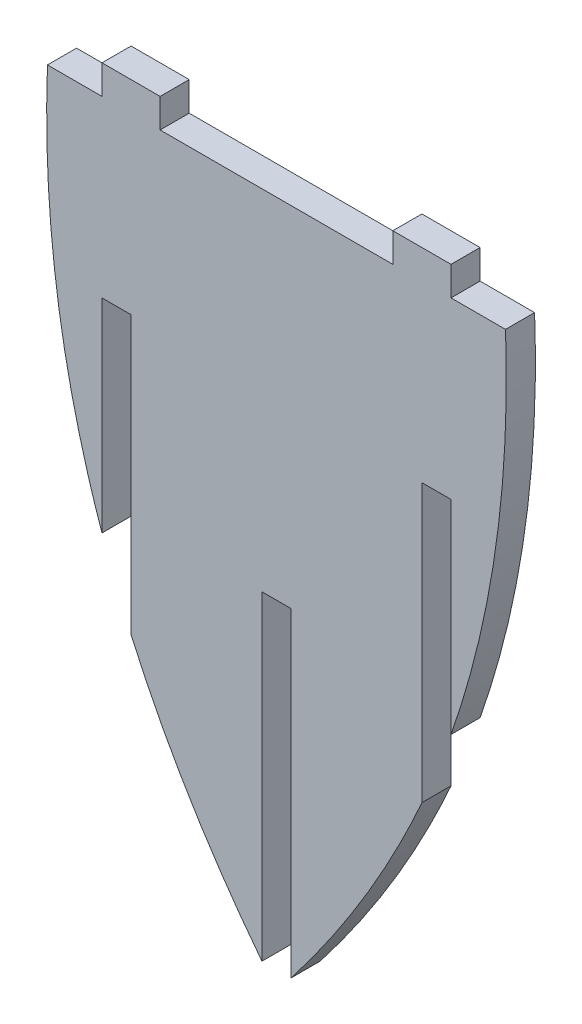
SolidWorks part; units mm, degrees
ref_plane "Front Plane" through (0, 0, 0) normal (0, 0, 1) x (1, 0, 0)
ref_plane "Top Plane" through (0, 0, 0) normal (0, 1, 0) x (1, 0, 0)
ref_plane "Right Plane" through (0, 0, 0) normal (1, 0, 0) x (0, 0, -1)
sketch "Sketch1" plane through (0, 0, 0) normal (0, 0, 1) x (1, 0, 0)
  line L0 (-53.175, 406.4) -> (-41.275, 406.4)
  line L1 (-41.275, 412.75) -> (-28.575, 412.75)
  line L2 (-34.925, 368.3) -> (-34.925, 307.7927)
  line L3 (-41.275, 323.85) -> (-41.275, 368.3)
  line L4 (-41.275, 368.3) -> (-34.925, 368.3)
  line L5 (-53.175, 406.4) -> (-8.275, 406.4) construction
  line L6 (-41.275, 406.4) -> (-41.275, 412.75)
  line L7 (-6.35, 260.35) -> (-6.35, 330.2)
  line L8 (-28.575, 412.75) -> (-28.575, 406.4)
  line L9 (-28.575, 406.4) -> (-6.35, 406.4)
  line L10 (-3.175, 274.1399) -> (-3.175, 422.7876) construction
  line L11 (22.225, 412.75) -> (34.925, 412.75)
  line L12 (22.225, 412.75) -> (22.225, 406.4)
  line L13 (-6.35, 330.2) -> (0, 330.2)
  line L14 (34.925, 406.4) -> (34.925, 412.75)
  line L15 (22.225, 406.4) -> (-6.35, 406.4)
  line L16 (34.925, 406.4) -> (46.825, 406.4)
  line L17 (0, 330.2) -> (0, 260.35)
  line L18 (28.575, 368.3) -> (28.575, 307.7927)
  line L19 (34.925, 368.3) -> (28.575, 368.3)
  line L20 (34.925, 323.85) -> (34.925, 368.3)
  spline S0 degree 2 poles (-53.175, 406.4) (-54.7945, 362.5913) (-41.275, 323.85) knots 0 0 0 0.535069 0.535069 0.535069
  spline S1 degree 2 poles (46.825, 406.4) (48.4445, 362.5913) (34.925, 323.85) knots 0 0 0 0.535069 0.535069 0.535069
  spline S2 degree 2 poles (-34.925, 307.7927) (-23.9227, 282.9717) (-6.35, 260.35) knots 0.6475 0.6475 0.6475 1 1 1
  spline S3 degree 2 poles (28.575, 307.7927) (17.5727, 282.9717) (0, 260.35) knots 0.6475 0.6475 0.6475 1 1 1
  dimension "D1" = 38.1
  dimension "D2" = 38.1
  dimension "D3" = 25.4
  dimension "D4" = 82.55
  dimension "D5" = 3.175
  dimension "D6" = 38.1
  dimension "D7" = 6.35
extrude "Boss-Extrude1" add sketch "Sketch1" along normal blind 6.35
